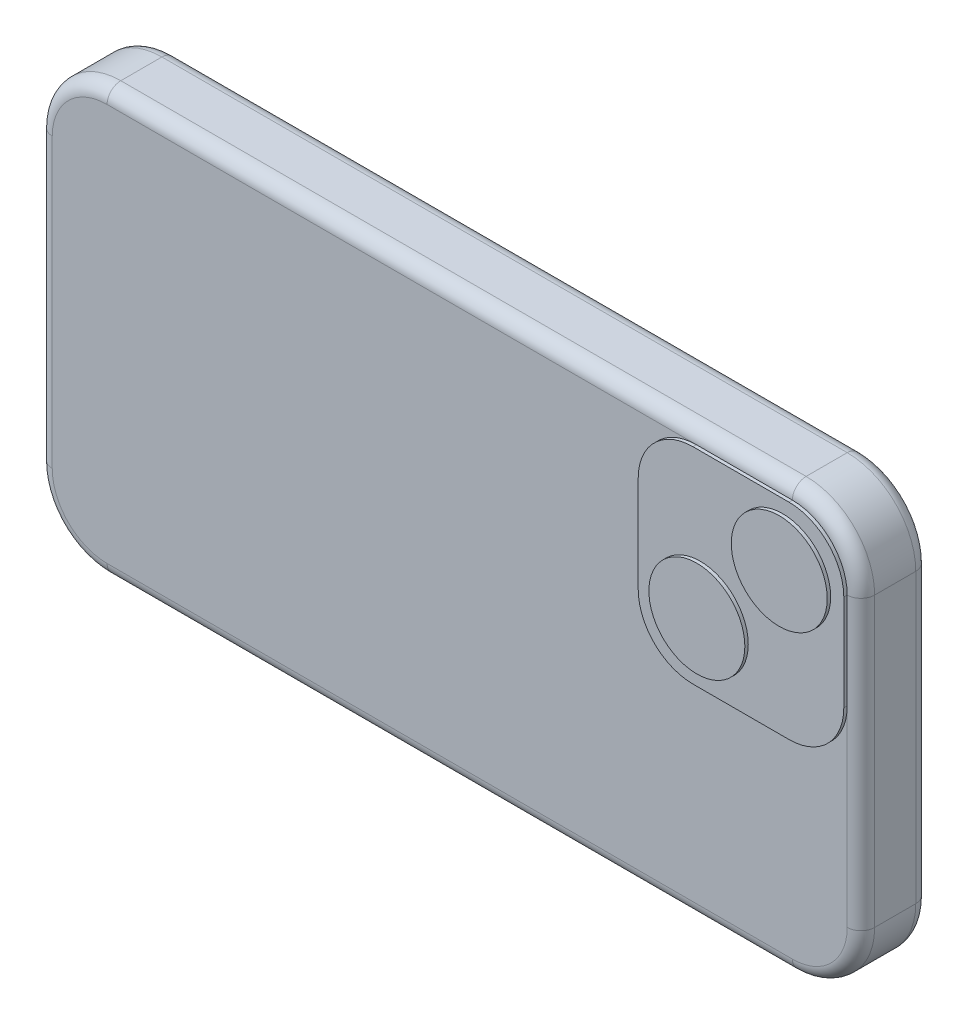
SolidWorks part; units mm, degrees
ref_plane "Front Plane" through (0, 0, 0) normal (0, 0, 1) x (1, 0, 0)
ref_plane "Top Plane" through (0, 0, 0) normal (0, 1, 0) x (1, 0, 0)
ref_plane "Right Plane" through (0, 0, 0) normal (1, 0, 0) x (0, 0, -1)
sketch "Sketch1" plane through (0, 0, 0) normal (0, 0, 1) x (1, 0, 0)
  line L1 (-76.2, -39.37) -> (76.2, -39.37)
  line L2 (-76.2, -39.37) -> (-76.2, 39.37)
  line L3 (-76.2, 39.37) -> (76.2, 39.37)
  line L4 (76.2, -39.37) -> (76.2, 39.37)
  line L5 (-76.2, -39.37) -> (76.2, 39.37) construction
  line L6 (-76.2, 39.37) -> (76.2, -39.37) construction
  point P0 (0, 0)
  dimension "D1" = 78.74
  dimension "D2" = 152.4
extrude "Boss-Extrude1" add sketch "Sketch1" along normal mid plane 12.7
fillet "Fillet1" radius 12.7 4 edges at (76.2, 39.37, 0) (76.2, -39.37, 0) (-76.2, -39.37, 0) (-76.2, 39.37, 0)
fillet "Fillet2" radius 2.54 16 edges at (-72.4803, 35.6503, -6.35) (-76.2, 0, -6.35) (-72.4803, -35.6503, -6.35) (0, -39.37, -6.35) (72.4803, -35.6503, -6.35) (76.2, 0, -6.35) (72.4803, 35.6503, -6.35) (0, 39.37, -6.35) (72.4803, -35.6503, 6.35) (0, -39.37, 6.35) (-72.4803, -35.6503, 6.35) (-76.2, 0, 6.35) (-72.4803, 35.6503, 6.35) (0, 39.37, 6.35) (72.4803, 35.6503, 6.35) (76.2, 0, 6.35)
sketch "Sketch2" plane through (0, 0, 6.35) normal (0, 0, 1) x (1, 0, 0)
  line L1 (63.5, 36.83) -> (45.72, 36.83)
  line L2 (73.66, 26.67) -> (73.66, 8.89)
  line L3 (63.5, -1.27) -> (45.72, -1.27)
  line L4 (-63.5, -36.83) -> (63.5, -36.83)
  line L5 (73.66, -26.67) -> (73.66, 26.67)
  line L6 (63.5, 36.83) -> (-63.5, 36.83)
  line L7 (-73.66, 26.67) -> (-73.66, -26.67)
  line L9 (73.66, 8.89) -> (73.66, 26.67)
  line L10 (63.5, 36.83) -> (45.72, 36.83)
  line L12 (35.56, 26.67) -> (35.56, 8.89)
  arc A0 (73.66, 8.89) -> (63.5, -1.27) centre (63.5, 8.89) cw
  arc A1 (35.56, 8.89) -> (45.72, -1.27) centre (45.72, 8.89) ccw
  arc A2 (45.72, 36.83) -> (35.56, 26.67) centre (45.72, 26.67) ccw
  arc A4 (63.5, -36.83) -> (73.66, -26.67) centre (63.5, -26.67) ccw
  arc A5 (73.66, 26.67) -> (63.5, 36.83) centre (63.5, 26.67) ccw
  arc A6 (-63.5, 36.83) -> (-73.66, 26.67) centre (-63.5, 26.67) ccw
  arc A7 (-73.66, -26.67) -> (-63.5, -36.83) centre (-63.5, -26.67) ccw
  arc A9 (73.66, 26.67) -> (63.5, 36.83) centre (63.5, 26.67) ccw
  point P17 (73.66, -1.27)
  point P20 (35.56, -1.27)
  point P23 (35.56, 36.83)
  line M15 (73.66, -26.67) -> (73.66, 26.67)
  arc M16 (73.66, 26.67) -> (63.5, 36.83) centre (63.5, 26.67) ccw
  line M17 (63.5, 36.83) -> (-63.5, 36.83)
  dimension "D4" = 10.16
  dimension "D2" = 38.1
  dimension "D3" = 38.1
  dimension "D1" = 0
extrude "Boss-Extrude2" add sketch "Sketch2" along normal mid plane 1.27 contours A2 L12 A1 L3 A0 M17 M15 M16
sketch "Sketch3" plane through (0, 0, 6.985) normal (0, 0, 1) x (1, 0, 0)
  line L0 (70.6842, 33.8542) -> (38.5358, 1.7058) construction
  arc A0 (73.66, 26.67) -> (63.5, 36.83) centre (63.5, 26.67) ccw construction
  arc A1 (35.56, 8.89) -> (45.72, -1.27) centre (45.72, 8.89) ccw construction
  circle A2 centre (62.3335, 25.5035) radius 8.89
  circle A3 centre (47.067, 10.237) radius 8.89
  dimension "D1" = 17.78
  dimension "D2" = 17.78
  dimension "D3" = 21.59
  dimension "D4" = 12.065
extrude "Boss-Extrude3" add sketch "Sketch3" along normal mid plane 1.27
